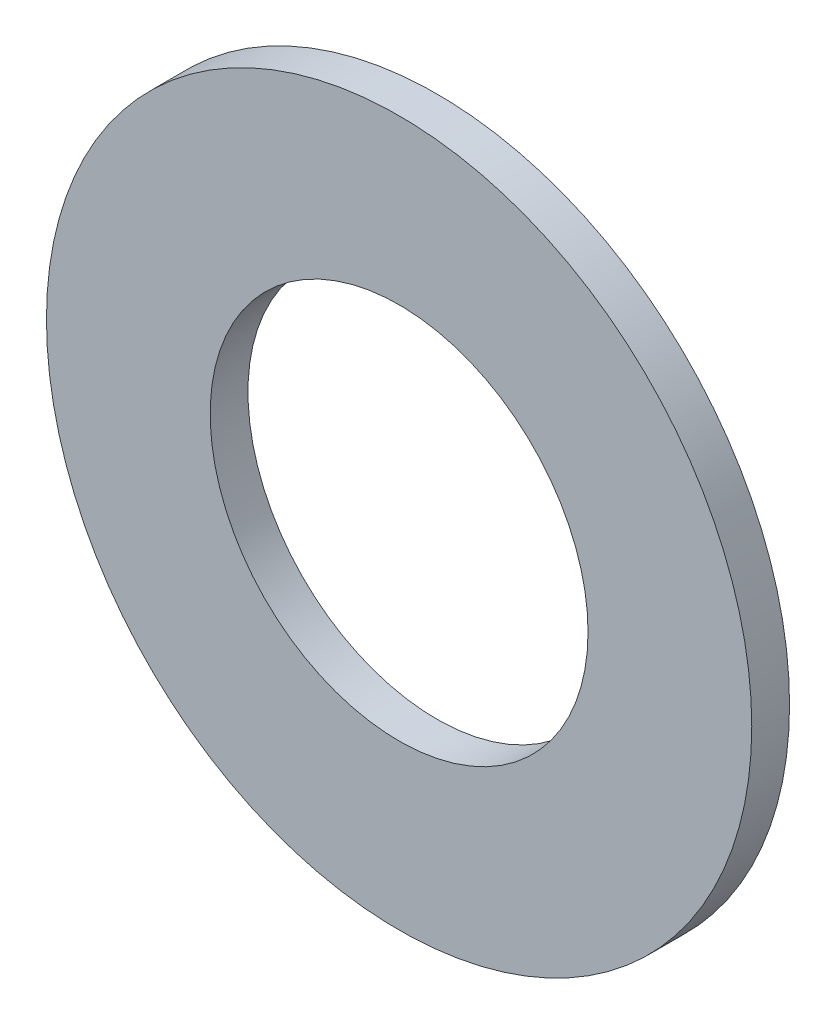
SolidWorks part; units mm, degrees
material "PMMA"
ref_plane "Front Plane" through (0, 0, 0) normal (0, 0, 1) x (1, 0, 0)
ref_plane "Top Plane" through (0, 0, 0) normal (0, 1, 0) x (1, 0, 0)
ref_plane "Right Plane" through (0, 0, 0) normal (1, 0, 0) x (0, 0, -1)
sketch "Sketch1" plane through (0, 0, 0) normal (0, 0, 1) x (1, 0, 0)
  circle A0 centre (0, 0) radius 7.5
  circle A1 centre (0, 0) radius 14
  dimension "D1" = 15
  dimension "D2" = 28
extrude "Boss-Extrude1" add sketch "Sketch1" along normal blind 1.5
